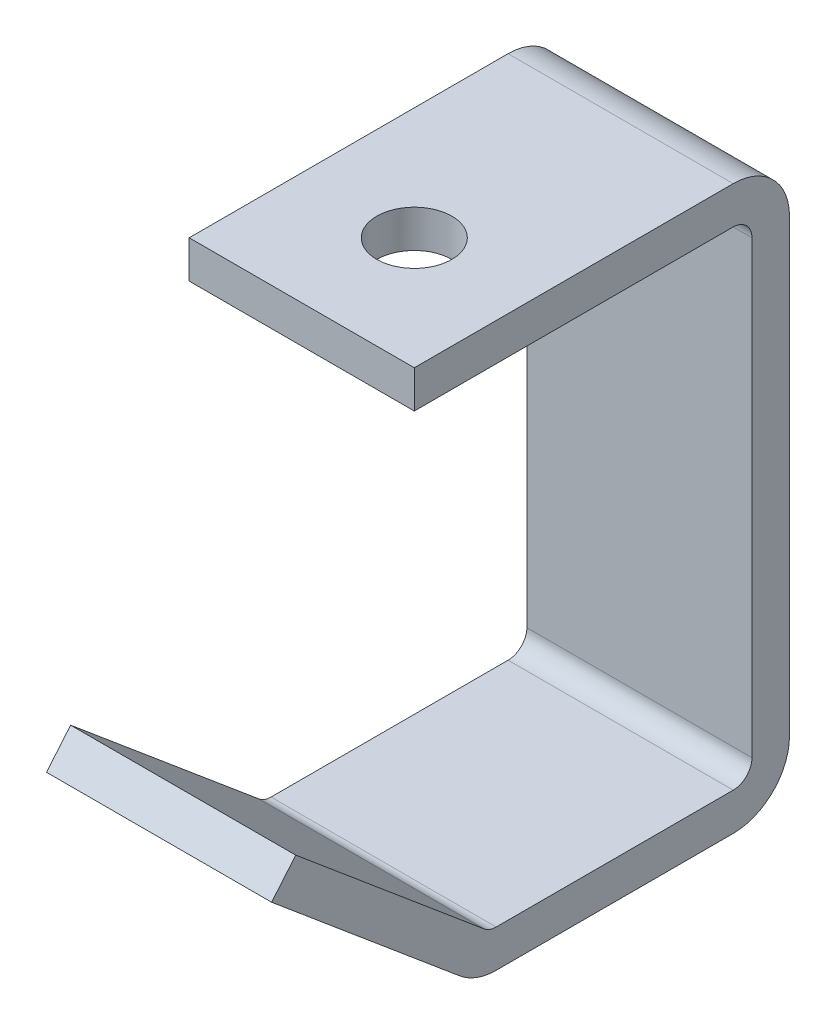
SolidWorks part; units mm, degrees
ref_plane "front" through (0, 0, 0) normal (0, 0, 1) x (1, 0, 0)
ref_plane "top" through (0, 0, 0) normal (0, 1, 0) x (1, 0, 0)
ref_plane "right" through (0, 0, 0) normal (1, 0, 0) x (0, 0, -1)
sketch "Sketch1" plane through (0, 0, 0) normal (1, 0, 0) x (0, 0, -1)
  line L0 (0, 0) -> (0, 82.55)
  line L1 (0, 82.55) -> (-57.15, 82.55)
  line L4 (-77.2165, 27.4943) -> (-44.45, 0)
  line L5 (-44.45, 0) -> (0, 0)
  dimension "D1" = 82.55
  dimension "D2" = 57.15
  dimension "D3" = 40
  dimension "D4" = 42.7736
  dimension "D5" = 44.45
extrude "Base-Extrude-Thin" add sketch "Sketch1" along normal mid plane 38.1 thin
sketch "Sketch2" plane through (0, 88.9, 0) normal (0, 1, 0) x (-1, 0, 0)
  line L0 (0, 50) -> (0, -50) construction
  line L1 (-19.05, 57.15) -> (19.05, 57.15) construction
  circle A0 centre (0, 38.1) radius 6.35
  dimension "D1" = 12.7
  dimension "D2" = 19.05
extrude "Cut-Extrude1" cut sketch "Sketch2" against normal up to next
